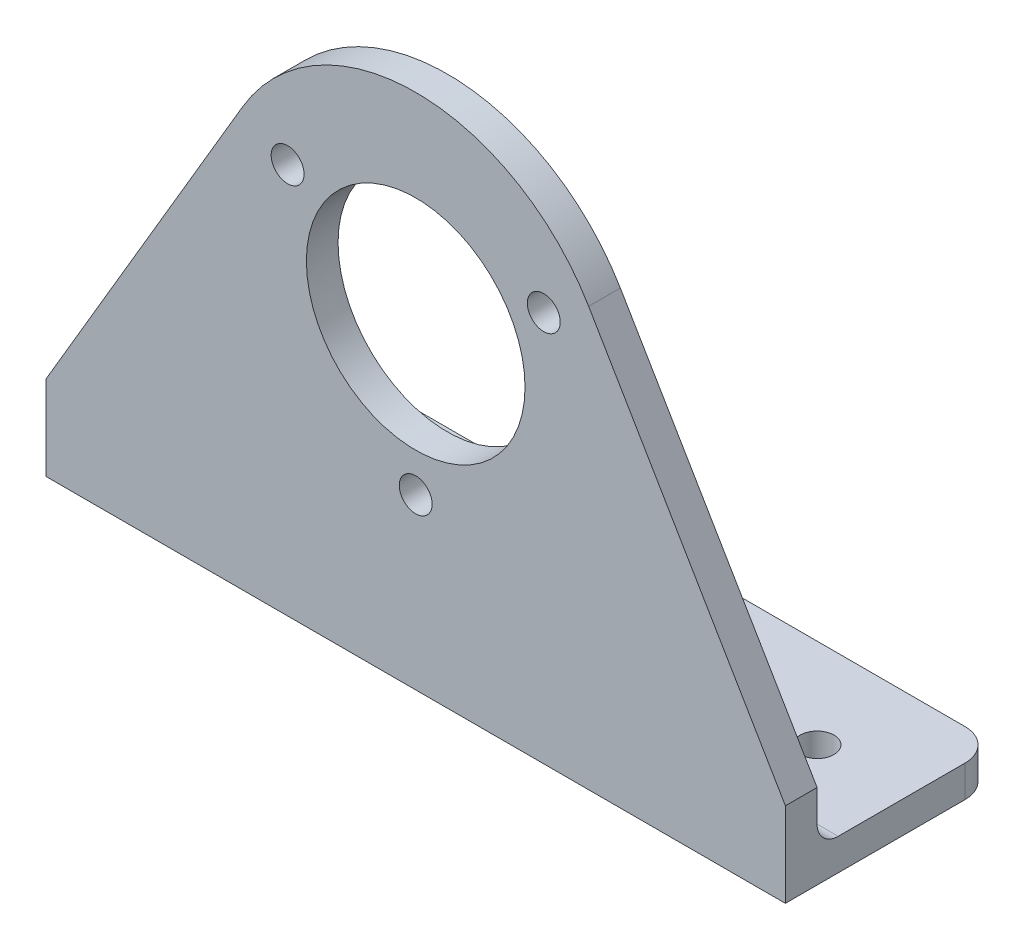
SolidWorks part; units mm, degrees
ref_plane "Front Plane" through (0, 0, 0) normal (0, 0, 1) x (1, 0, 0)
ref_plane "Top Plane" through (0, 0, 0) normal (0, 1, 0) x (1, 0, 0)
ref_plane "Right Plane" through (0, 0, 0) normal (1, 0, 0) x (0, 0, -1)
sketch "Sketch1" plane through (0, 0, 0) normal (0, 1, 0) x (1, 0, 0)
  line L1 (0, 0) -> (70, 0)
  line L2 (0, 0) -> (0, 17)
  line L3 (0, 17) -> (70, 17)
  line L4 (70, 0) -> (70, 17)
  dimension "D1" = 70
  dimension "D2" = 17
extrude "Boss-Extrude1" add sketch "Sketch1" along normal blind 3
sketch "Sketch2" plane through (0, 0, 0) normal (0, 0, 1) x (1, 0, 0)
  line L0 (0, 0) -> (70, 0)
  line L1 (11, 0) -> (-11, 0) construction
  line L2 (70, 3) -> (70, 0) construction
  line L3 (70, 0) -> (70, 8)
  line L4 (0, 8) -> (18.6267, 39.6393)
  line L5 (54, 30) -> (16, 30) construction
  line L6 (70, 8) -> (51.3733, 39.6393)
  line L7 (0, -1.65) -> (0, 1.65) construction
  line L8 (0, 8) -> (0, 0)
  arc A0 (51.3733, 39.6393) -> (18.6267, 39.6393) centre (35, 30) ccw
  circle A1 centre (35, 30) radius 10.35
  circle A2 centre (35, 30) radius 14 construction
  circle A3 centre (35, 16) radius 1.5591
  circle A4 centre (22.8756, 37) radius 1.5591
  circle A5 centre (47.1244, 37) radius 1.5591
  point P28 (35, 30)
  dimension "D4" = 38
  dimension "D5" = 20.7
  dimension "D6" = 28
  dimension "D7" = 3.1183
  dimension "D1" = 8
  dimension "D2" = 8
  dimension "D3" = 30
  dimension "D9" = 35
  dimension "D8" = 3
extrude "Boss-Extrude2" add sketch "Sketch2" along normal blind 3
sketch "Sketch3" plane through (0, 3, 0) normal (0, 1, 0) x (1, 0, 0)
  line L0 (70, 17) -> (0, 17) construction
  line L1 (0, -11) -> (0, 11) construction
  line L2 (70, 0) -> (70, 17) construction
  circle A0 centre (8.5, 8.5) radius 1.6
  circle A1 centre (61.5, 8.5) radius 1.6
  dimension "D5" = 3.2
  dimension "D6" = 3.2
  dimension "D1" = 8.5
  dimension "D2" = 8.5
  dimension "D3" = 8.5
  dimension "D4" = 8.5
extrude "Cut-Extrude1" cut sketch "Sketch3" against normal through all
fillet "Fillet1" radius 3 2 edges at (70, 1.5, -17) (0, 1.5, -17)
fillet "Fillet2" radius 2 1 edges
